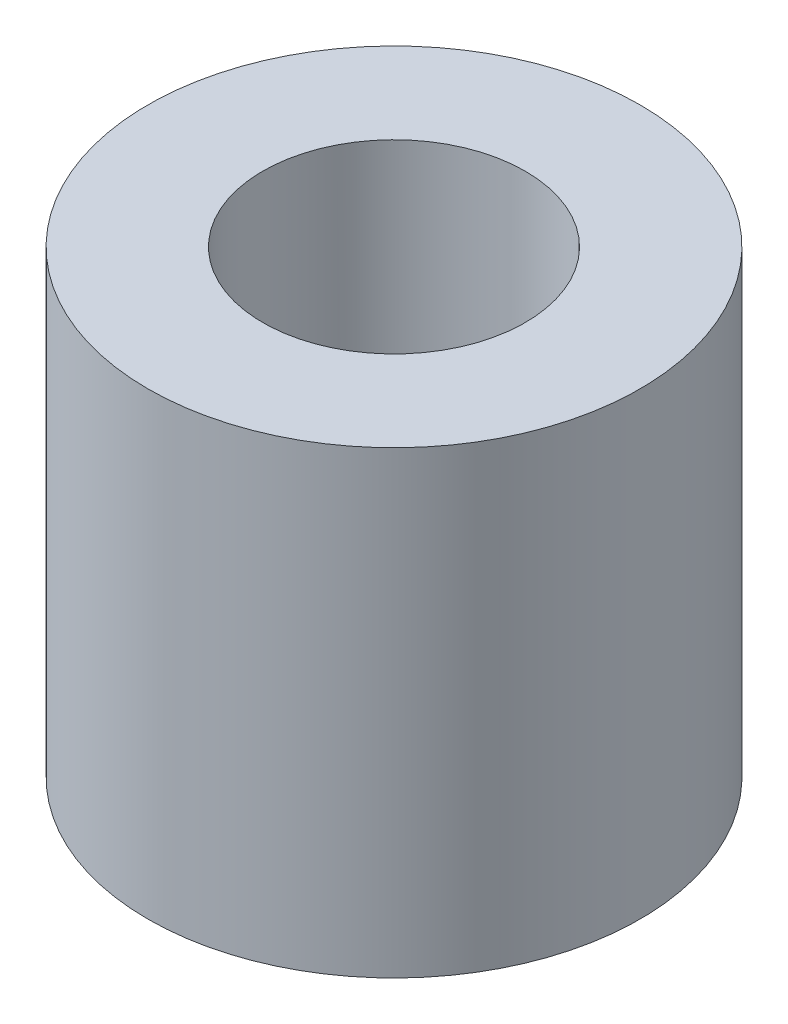
SolidWorks part; units mm, degrees
ref_plane "Front" through (0, 0, 0) normal (0, 0, 1) x (1, 0, 0)
ref_plane "Top" through (0, 0, 0) normal (0, 1, 0) x (1, 0, 0)
ref_plane "Right" through (0, 0, 0) normal (1, 0, 0) x (0, 0, -1)
sketch "Sketch1" plane through (0, 0, 0) normal (0, 1, 0) x (1, 0, 0)
  circle A0 centre (0, 0) radius 7.5
  dimension "D1" = 15
extrude "Extrude1" add sketch "Sketch1" along normal blind 14
sketch "Sketch2" plane through (0, 0, 0) normal (0, 0, 1) x (1, 0, 0)
  line L0 (0, 0) -> (0, 15.7428) construction
  line L1 (0, 14) -> (4, 14)
  line L2 (7.5, 14) -> (-7.5, 14) construction
  line L3 (4, 14) -> (4, 4)
  line L4 (4, 4) -> (0, 1.6906)
  line L5 (0, 1.6906) -> (0, 14)
  dimension "D1" = 10
  dimension "D2" = 60
  dimension "D3" = 8
revolve "Cut-Revolve1" cut sketch "Sketch2" angle 360 about L0
